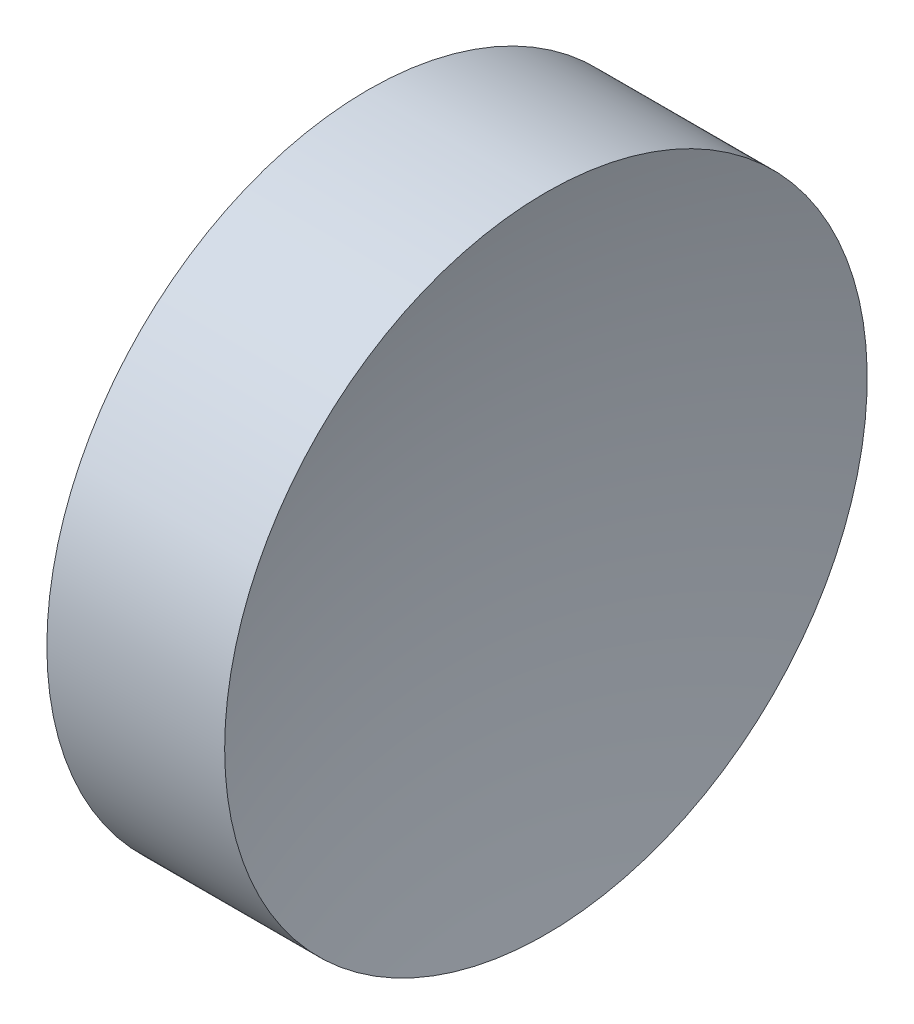
SolidWorks part; units mm, degrees
ref_plane "前视基准面" through (0, 0, 0) normal (0, 0, 1) x (1, 0, 0)
ref_plane "上视基准面" through (0, 0, 0) normal (0, 1, 0) x (1, 0, 0)
ref_plane "右视基准面" through (0, 0, 0) normal (1, 0, 0) x (0, 0, -1)
sketch "草图1" plane through (0, 0, 0) normal (0, 0, 1) x (1, 0, 0)
  line L0 (109.9369, 65.2226) -> (130.1809, 65.2226) construction
  line L1 (121.8527, 65.2226) -> (118.3527, 65.2226)
  line L3 (120.1027, 77.9226) -> (123.6167, 77.9226)
  line L4 (120.1027, 77.9226) -> (116.5887, 77.9226)
  arc A0 (118.3527, 65.2226) -> (116.5887, 77.9226) centre (71.7527, 65.2226) ccw
  arc A1 (123.6167, 77.9226) -> (121.8527, 65.2226) centre (168.4527, 65.2226) ccw
revolve "旋转1" add sketch "草图1" angle 360 about L0
